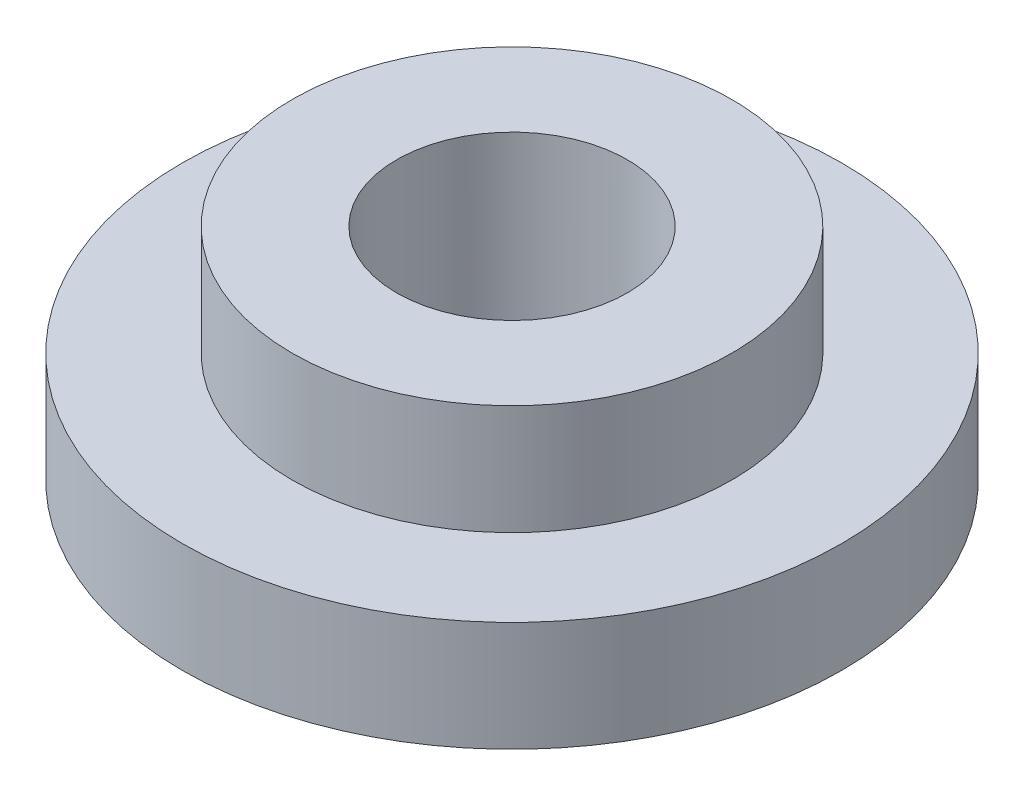
SolidWorks part; units mm, degrees
ref_plane "Front Plane" through (0, 0, 0) normal (0, 0, 1) x (1, 0, 0)
ref_plane "Top Plane" through (0, 0, 0) normal (0, 1, 0) x (1, 0, 0)
ref_plane "Right Plane" through (0, 0, 0) normal (1, 0, 0) x (0, 0, -1)
sketch "Sketch1" plane through (0, 0, 0) normal (0, 1, 0) x (1, 0, 0)
  circle A0 centre (0, 0) radius 6
extrude "Boss-Extrude1" add sketch "Sketch1" along normal blind 2
sketch "Sketch2" plane through (0, 2, 0) normal (0, 1, 0) x (1, 0, 0)
  circle A0 centre (0, 0) radius 4
extrude "Boss-Extrude2" add sketch "Sketch2" along normal blind 2
sketch "Sketch3" plane through (0, 4, 0) normal (0, 1, 0) x (1, 0, 0)
  circle A0 centre (0, 0) radius 2.1
extrude "Cut-Extrude1" cut sketch "Sketch3" against normal through all both and the other way through all
sketch "Sketch4" plane through (0, 0, 0) normal (0, -1, 0) x (1, 0, 0)
  circle A1 centre (0, 0) radius 3.5
  circle A2 centre (0, 0) radius 2.1 construction
  circle A3 centre (0, 0) radius 2.1
extrude "Boss-Extrude3" add sketch "Sketch4" along normal blind 1
